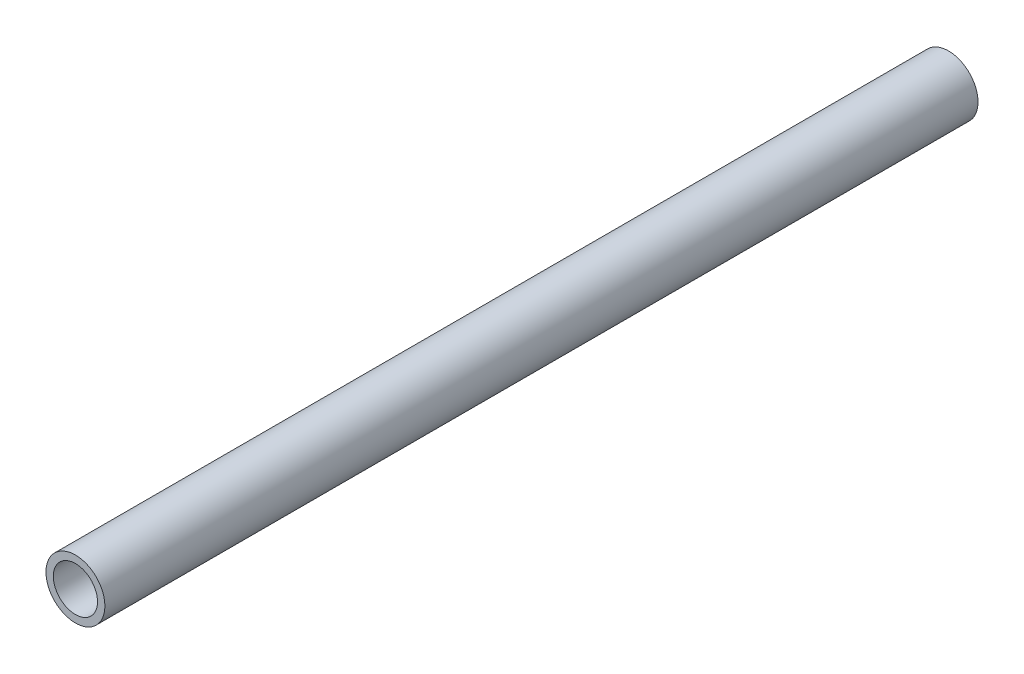
SolidWorks part; units mm, degrees
material "亚克力"
ref_plane "前视基准面" through (0, 0, 0) normal (0, 0, 1) x (1, 0, 0)
ref_plane "上视基准面" through (0, 0, 0) normal (0, 1, 0) x (1, 0, 0)
ref_plane "右视基准面" through (0, 0, 0) normal (1, 0, 0) x (0, 0, -1)
sketch "草图1" plane through (0, 0, 0) normal (0, 0, 1) x (1, 0, 0)
  circle A0 centre (0, 0) radius 6
  circle A1 centre (0, 0) radius 8
  dimension "D1" = 12
  dimension "D2" = 16
extrude "凸台-拉伸1" add sketch "草图1" along normal blind 237
